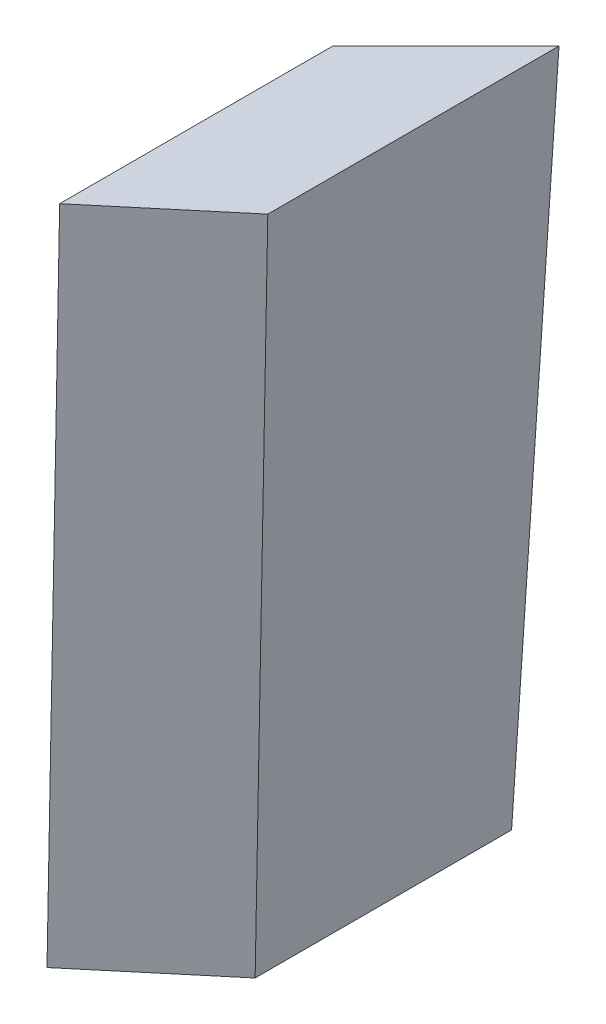
SolidWorks part; units mm, degrees
ref_plane "Alzado" through (0, 0, 0) normal (0, 0, 1) x (1, 0, 0)
ref_plane "Planta" through (0, 0, 0) normal (0, 1, 0) x (1, 0, 0)
ref_plane "Vista lateral" through (0, 0, 0) normal (1, 0, 0) x (0, 0, -1)
sketch "Croquis1" plane through (0, 0, 0) normal (0, 1, 0) x (1, 0, 0)
  line L0 (0, 0) -> (0, 26.32)
  line L1 (0, 26.32) -> (12.4958, 38.8275)
  line L2 (12.4958, 38.8275) -> (12.4958, 10.4975)
  line L3 (12.4958, 10.4975) -> (0, 0)
  dimension "D1" = 26.32
  dimension "D2" = 28.33
  dimension "D3" = 16.32
  dimension "D4" = 17.68
ref_plane "Plano1" through (0, 75, 0) normal (0, 1, 0) x (1, 0, 0)
sketch "Croquis3" plane through (0, 0, 0) normal (0, 0, -1) x (-1, 0, 0)
  line L0 (0, 0) -> (0, 79.2158) construction
  line L1 (0, 0) -> (2.7675, 79.251)
  dimension "D1" = 2
sketch "Croquis2" plane through (0, 75, 0) normal (0, 1, 0) x (1, 0, 0)
  line L0 (2.62, -1.22) -> (15.1158, 9.2775)
  line L1 (15.1158, 9.2775) -> (15.1158, 41.4475)
  line L2 (15.1158, 41.4475) -> (2.62, 28.94)
  line L3 (2.62, 28.94) -> (2.62, -1.22)
  line L4 (0, 0) -> (2.62, 0)
  line L5 (2.62, 0) -> (2.62, 2.62)
  line L6 (0, 26.32) -> (2.62, 26.32)
  line L7 (2.62, 26.32) -> (2.62, 28.94)
  dimension "D1" = 32.17
  dimension "D2" = 30.16
  dimension "D3" = 17.68
  dimension "D4" = 16.32
  dimension "D5" = 2.62
  dimension "D6" = 2.62
  dimension "D7" = 2.62
loft "Recubrir1" add profiles "Croquis1" section "Croquis1" section "Croquis2"
